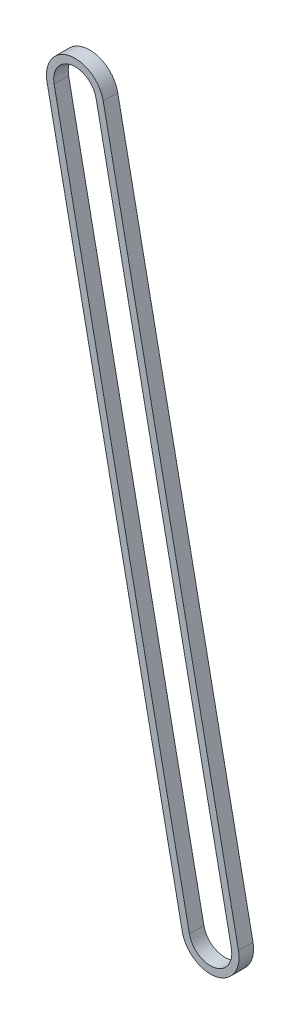
SolidWorks part; units mm, degrees
ref_plane "Front Plane" through (0, 0, 0) normal (0, 0, 1) x (1, 0, 0)
ref_plane "Top Plane" through (0, 0, 0) normal (0, 1, 0) x (1, 0, 0)
ref_plane "Right Plane" through (0, 0, 0) normal (1, 0, 0) x (0, 0, -1)
sketch "Sketch2" plane through (0, 0, 0) normal (0, 0, 1) x (1, 0, 0)
  line L0 (0, 0) -> (1, 0) construction
  line L1 (0, 0) -> (0, 1) construction
  line L2 (5.7827, 1.1705) -> (43.0288, -182.8403)
  line L3 (31.4633, -185.1813) -> (-5.7827, -1.1705)
  arc A0 (-5.7827, -1.1705) -> (5.7827, 1.1705) centre (0, 0) cw
  arc A1 (43.0288, -182.8403) -> (31.4633, -185.1813) centre (37.246, -184.0108) cw
sketch "Sketch3" plane through (0, 0, 0) normal (0, 0, 1) x (1, 0, 0)
  line L4 (44.989, -182.4436) -> (7.743, 1.5673)
  line L5 (-7.743, -1.5673) -> (29.503, -185.5781)
  line L6 (44.989, -182.4436) -> (7.743, 1.5673)
  line L7 (-7.743, -1.5673) -> (29.503, -185.5781)
  arc A4 (7.743, 1.5673) -> (-7.743, -1.5673) centre (0, 0) ccw
  arc A5 (29.503, -185.5781) -> (44.989, -182.4436) centre (37.246, -184.0108) ccw
  arc A6 (7.743, 1.5673) -> (-7.743, -1.5673) centre (0, 0) ccw
  arc A7 (29.503, -185.5781) -> (44.989, -182.4436) centre (37.246, -184.0108) ccw
  dimension "D1" = 2
extrude "Boss-Extrude1" add sketch "Sketch3" along normal blind 4
sketch "Sketch4" plane through (0, 0, 4) normal (0, 0, 1) x (1, 0, 0)
  line L4 (43.0288, -182.8403) -> (5.7827, 1.1705)
  line L5 (-5.7827, -1.1705) -> (31.4633, -185.1813)
  line L6 (43.0288, -182.8403) -> (5.7827, 1.1705)
  line L7 (-5.7827, -1.1705) -> (31.4633, -185.1813)
  arc A4 (31.4633, -185.1813) -> (43.0288, -182.8403) centre (37.246, -184.0108) ccw
  arc A5 (5.7827, 1.1705) -> (-5.7827, -1.1705) centre (0, 0) ccw
  arc A6 (31.4633, -185.1813) -> (43.0288, -182.8403) centre (37.246, -184.0108) ccw
  arc A7 (5.7827, 1.1705) -> (-5.7827, -1.1705) centre (0, 0) ccw
  dimension "D1" = 2
extrude "Cut-Extrude1" cut sketch "Sketch4" against normal blind 4
